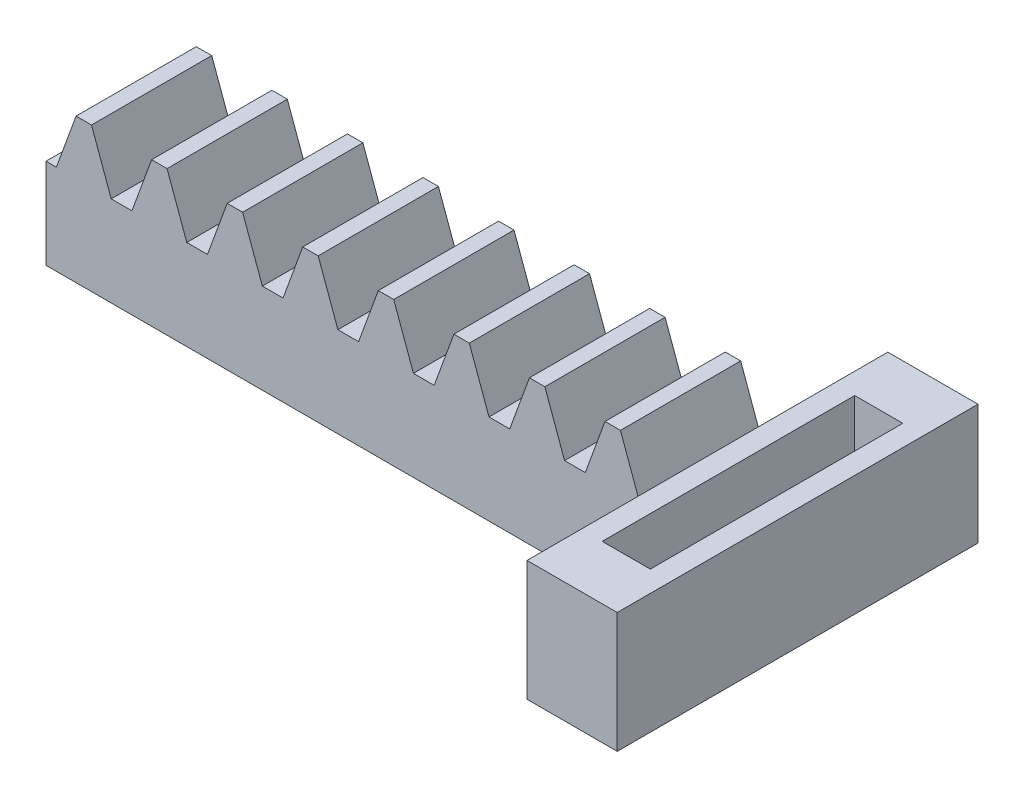
SolidWorks part; units mm, degrees
ref_plane "Front Plane" through (0, 0, 0) normal (0, 0, 1) x (1, 0, 0)
ref_plane "Top Plane" through (0, 0, 0) normal (0, 1, 0) x (1, 0, 0)
ref_plane "Right Plane" through (0, 0, 0) normal (1, 0, 0) x (0, 0, -1)
ref_plane "Plane1" through (0, 0, -10.0478) normal (0, 0, -1) x (-1, 0, 0)
sketch "Sketch1" plane through (0, 0, -10.0478) normal (0, 0, -1) x (-1, 0, 0)
  line L0 (24.6055, 10.6198) -> (22.9677, 6.1198)
  line L1 (22.9677, 6.1198) -> (22.3713, 6.1198)
  line L2 (22.3713, 6.1198) -> (22.3713, -1.3802)
  line L3 (22.3713, -1.3802) -> (72.3713, -1.3802)
  line L4 (72.3713, -1.3802) -> (72.3713, 6.1198)
  line L5 (72.3713, 6.1198) -> (71.5094, 6.1198)
  line L6 (71.5094, 6.1198) -> (69.8715, 10.6198)
  line L7 (69.8715, 10.6198) -> (68.5878, 10.6198)
  line L8 (68.5878, 10.6198) -> (66.95, 6.1198)
  line L9 (66.95, 6.1198) -> (65.2262, 6.1198)
  line L10 (65.2262, 6.1198) -> (63.5884, 10.6198)
  line L11 (63.5884, 10.6198) -> (62.3046, 10.6198)
  line L12 (62.3046, 10.6198) -> (60.6668, 6.1198)
  line L13 (60.6668, 6.1198) -> (58.943, 6.1198)
  line L14 (58.943, 6.1198) -> (57.3052, 10.6198)
  line L15 (57.3052, 10.6198) -> (56.0215, 10.6198)
  line L16 (56.0215, 10.6198) -> (54.3836, 6.1198)
  line L17 (54.3836, 6.1198) -> (52.6598, 6.1198)
  line L18 (52.6598, 6.1198) -> (51.022, 10.6198)
  line L19 (51.022, 10.6198) -> (49.7383, 10.6198)
  line L20 (49.7383, 10.6198) -> (48.1004, 6.1198)
  line L21 (48.1004, 6.1198) -> (46.3767, 6.1198)
  line L22 (46.3767, 6.1198) -> (44.7388, 10.6198)
  line L23 (44.7388, 10.6198) -> (43.4551, 10.6198)
  line L24 (43.4551, 10.6198) -> (41.8172, 6.1198)
  line L25 (41.8172, 6.1198) -> (40.0935, 6.1198)
  line L26 (40.0935, 6.1198) -> (38.4556, 10.6198)
  line L27 (38.4556, 10.6198) -> (37.1719, 10.6198)
  line L28 (37.1719, 10.6198) -> (35.534, 6.1198)
  line L29 (35.534, 6.1198) -> (33.8103, 6.1198)
  line L30 (33.8103, 6.1198) -> (32.1724, 10.6198)
  line L31 (32.1724, 10.6198) -> (30.8887, 10.6198)
  line L32 (30.8887, 10.6198) -> (29.2508, 6.1198)
  line L33 (29.2508, 6.1198) -> (27.5271, 6.1198)
  line L34 (27.5271, 6.1198) -> (25.8892, 10.6198)
  line L35 (25.8892, 10.6198) -> (24.6055, 10.6198)
extrude "Boss-Extrude1" add sketch "Sketch1" against normal blind 10
sketch "Sketch2" plane through (-22.3713, 0, 0) normal (1, 0, 0) x (0, 0, -1)
  line L0 (-9.9522, 7.3698) -> (20.0478, 7.3698)
  line L1 (-9.9522, 7.3698) -> (-9.9522, -2.6302)
  line L2 (-9.9522, -2.6302) -> (20.0478, -2.6302)
  line L3 (20.0478, 7.3698) -> (20.0478, -2.6302)
extrude "Boss-Extrude2" add sketch "Sketch2" along normal blind 7.5
sketch "Sketch3" plane through (0, 7.3698, 0) normal (0, 1, 0) x (-1, 0, 0)
  line L0 (20.6213, -15.5478) -> (16.6213, -15.5478)
  line L1 (20.6213, -15.5478) -> (20.6213, 5.4522)
  line L2 (20.6213, 5.4522) -> (16.6213, 5.4522)
  line L3 (16.6213, -15.5478) -> (16.6213, 5.4522)
extrude "Cut-Extrude1" cut sketch "Sketch3" against normal up to next
